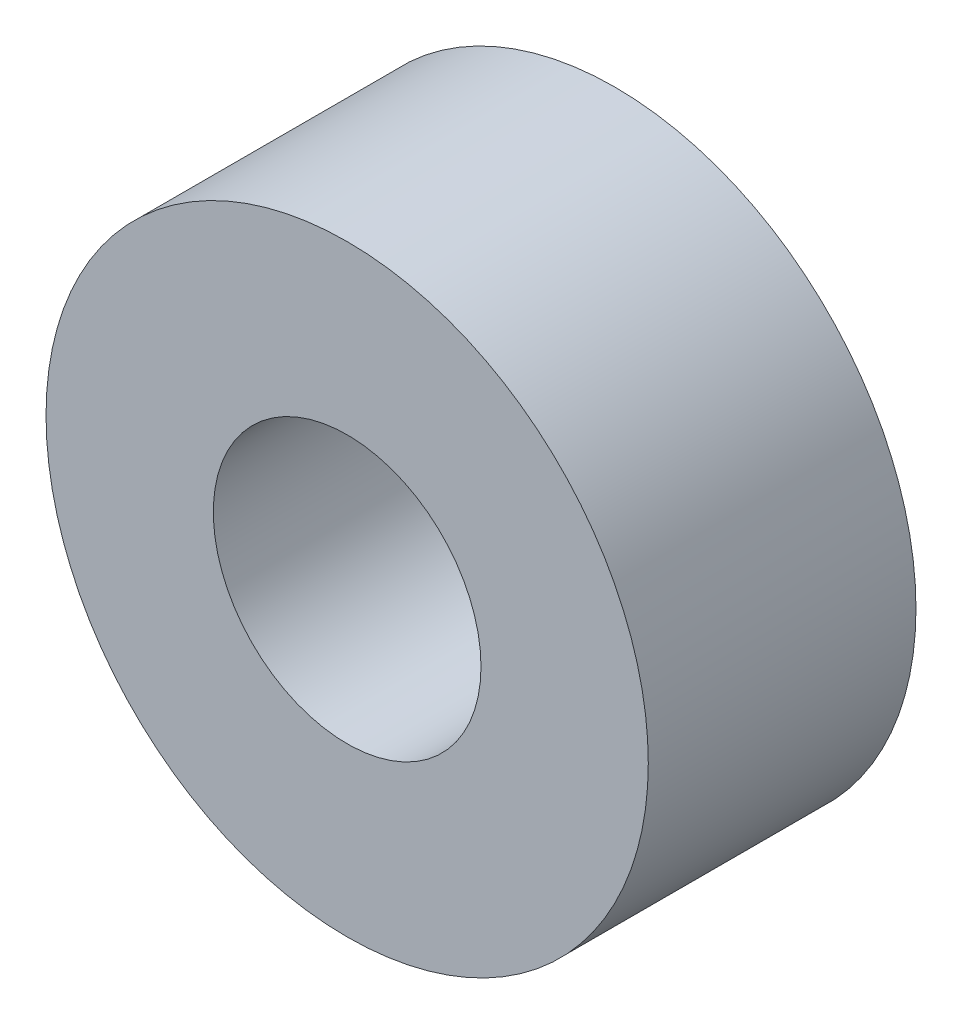
SolidWorks part; units mm, degrees
ref_plane "前视基准面" through (0, 0, 0) normal (0, 0, 1) x (1, 0, 0)
ref_plane "上视基准面" through (0, 0, 0) normal (0, 1, 0) x (1, 0, 0)
ref_plane "右视基准面" through (0, 0, 0) normal (1, 0, 0) x (0, 0, -1)
sketch "草图1" plane through (0, 0, 0) normal (0, 0, 1) x (1, 0, 0)
  circle A0 centre (0, 0) radius 2
  circle A1 centre (0, 0) radius 4.5
  dimension "D1" = 4
  dimension "D2" = 9
extrude "凸台-拉伸1" add sketch "草图1" along normal blind 4
